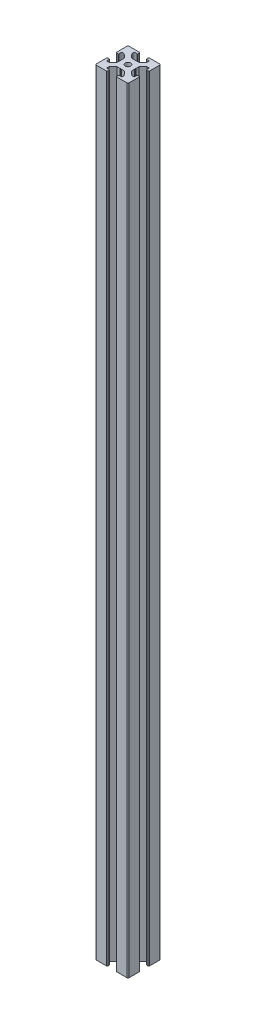
SolidWorks part; units mm, degrees
ref_plane "Front Plane" through (0, 0, 0) normal (0, 0, 1) x (1, 0, 0)
ref_plane "Top Plane" through (0, 0, 0) normal (0, 1, 0) x (1, 0, 0)
ref_plane "Right Plane" through (0, 0, 0) normal (1, 0, 0) x (0, 0, -1)
sketch "Sketch3" plane through (0, 0, 0) normal (0, 1, 0) x (1, 0, 0)
  line L0 (11, 30) -> (11, 27.75)
  line L1 (0, 0) -> (30, 0)
  line L2 (0, 0) -> (0, 30)
  line L3 (0, 30) -> (30, 30)
  line L4 (30, 0) -> (30, 30)
  line L5 (11, 27.75) -> (8, 27.75)
  line L6 (8, 27.75) -> (8, 25.5)
  line L7 (8, 25.5) -> (11.5, 21.75)
  line L8 (11.5, 21.75) -> (18.5, 21.75)
  line L9 (18.5, 21.75) -> (22, 25.5)
  line L10 (22, 25.5) -> (22, 27.75)
  line L11 (22, 27.75) -> (19, 27.75)
  line L12 (19, 27.75) -> (19, 30)
  line L13 (19, 30) -> (11, 30)
  line L14 (14.5, 21.75) -> (15, 21.25)
  line L15 (15, 21.25) -> (15.5, 21.75)
  line L16 (15.5, 21.75) -> (14.5, 21.75)
  line L17 (19, 29.5) -> (19, 30)
  line L18 (19.5, 30) -> (19, 30)
  line L19 (11, 29.5) -> (11, 30)
  line L20 (10.5, 30) -> (11, 30)
  line L21 (0, 19) -> (2.25, 19)
  line L22 (2.25, 19) -> (2.25, 22)
  line L23 (2.25, 22) -> (4.5, 22)
  line L24 (4.5, 22) -> (8.25, 18.5)
  line L25 (8.25, 18.5) -> (8.25, 11.5)
  line L26 (8.25, 11.5) -> (4.5, 8)
  line L27 (4.5, 8) -> (2.25, 8)
  line L28 (2.25, 8) -> (2.25, 11)
  line L29 (2.25, 11) -> (0, 11)
  line L30 (0, 11) -> (0, 19)
  line L31 (8.25, 15.5) -> (8.25, 14.5)
  line L32 (8.25, 14.5) -> (8.75, 15)
  line L33 (8.75, 15) -> (8.25, 15.5)
  line L34 (0.5, 19) -> (0, 19)
  line L35 (0, 19.5) -> (0, 19)
  line L36 (0, 10.5) -> (0, 11)
  line L37 (0.5, 11) -> (0, 11)
  line L38 (15, 30) -> (15, 0) construction
  line L39 (30, 15) -> (0, 15) construction
  line L40 (15, 8.75) -> (15.5, 8.25)
  line L41 (14.5, 8.25) -> (15, 8.75)
  line L42 (15.5, 8.25) -> (14.5, 8.25)
  line L43 (19.5, 0) -> (19, 0)
  line L44 (19, 0.5) -> (19, 0)
  line L45 (10.5, 0) -> (11, 0)
  line L46 (11, 0.5) -> (11, 0)
  line L47 (19, 2.25) -> (19, 0)
  line L48 (22, 2.25) -> (19, 2.25)
  line L49 (22, 4.5) -> (22, 2.25)
  line L50 (18.5, 8.25) -> (22, 4.5)
  line L51 (11.5, 8.25) -> (18.5, 8.25)
  line L52 (8, 4.5) -> (11.5, 8.25)
  line L53 (8, 2.25) -> (8, 4.5)
  line L54 (11, 2.25) -> (8, 2.25)
  line L55 (11, 0) -> (11, 2.25)
  line L56 (19, 0) -> (11, 0)
  line L57 (21.75, 14.5) -> (21.25, 15)
  line L58 (21.75, 15.5) -> (21.75, 14.5)
  line L59 (21.25, 15) -> (21.75, 15.5)
  line L60 (29.5, 11) -> (30, 11)
  line L61 (30, 10.5) -> (30, 11)
  line L62 (30, 19.5) -> (30, 19)
  line L63 (29.5, 19) -> (30, 19)
  line L64 (27.75, 11) -> (30, 11)
  line L65 (27.75, 8) -> (27.75, 11)
  line L66 (25.5, 8) -> (27.75, 8)
  line L67 (21.75, 11.5) -> (25.5, 8)
  line L68 (21.75, 18.5) -> (21.75, 11.5)
  line L69 (25.5, 22) -> (21.75, 18.5)
  line L70 (27.75, 22) -> (25.5, 22)
  line L71 (27.75, 19) -> (27.75, 22)
  line L72 (30, 19) -> (27.75, 19)
  line L73 (30, 11) -> (30, 19)
  arc A0 (19.5, 30) -> (19, 29.5) centre (19, 30) cw
  arc A1 (10.5, 30) -> (11, 29.5) centre (11, 30) ccw
  arc A2 (0.5, 19) -> (0, 19.5) centre (0, 19) ccw
  arc A3 (0.5, 11) -> (0, 10.5) centre (0, 11) cw
  arc A4 (19.5, 0) -> (19, 0.5) centre (19, 0) ccw
  arc A5 (10.5, 0) -> (11, 0.5) centre (11, 0) cw
  arc A6 (29.5, 11) -> (30, 10.5) centre (30, 11) ccw
  arc A7 (29.5, 19) -> (30, 19.5) centre (30, 19) cw
  point P7 (15, 21.75)
  point P16 (15, 30)
  point P26 (8.25, 15)
  point P35 (0, 15)
  dimension "D16" = 0.5
  dimension "D17" = 0.5
  dimension "D28" = 0.5
  dimension "D29" = 0.5
  dimension "D1" = 30
  dimension "D2" = 30
  dimension "D3" = 11
  dimension "D4" = 11
  dimension "D5" = 2.25
  dimension "D6" = 2.25
  dimension "D7" = 3
  dimension "D8" = 3
  dimension "D9" = 2.25
  dimension "D10" = 2.25
  dimension "D11" = 7
  dimension "D12" = 8.25
  dimension "D13" = 0.5
  dimension "D14" = 0.5
  dimension "D15" = 0.5
  dimension "D18" = 11
  dimension "D19" = 11
  dimension "D20" = 2.25
  dimension "D21" = 2.25
  dimension "D22" = 3
  dimension "D23" = 7
  dimension "D24" = 8.25
  dimension "D25" = 0.5
  dimension "D26" = 0.5
  dimension "D27" = 0.5
extrude "Boss-Extrude1" add sketch "Sketch3" along normal blind 710 contours L72 A7 L4 L3 A0 L12 L11 L10 L9 L8 L15 L14 L7 L6 L5 L0 A1 L2 A2 L21 L22 L23 L24 L25 L33 L32 L26 L27 L28 L29 A3 L1 A5 L55 L54 L53 L52 L51 L41 L40 L50 L49 L48 L47 A4
fillet "Fillet1" radius 1 4 edges at (0, 355, 0) (30, 355, 0) (30, 355, -30) (0, 355, -30)
sketch "Sketch4" plane through (0, 710, 0) normal (0, 1, 0) x (1, 0, 0)
  line L0 (18.5, 21.75) -> (8.25, 11.5) construction
  line L1 (21.75, 18.5) -> (11.5, 8.25) construction
  line L2 (15.5, 21.75) -> (21.75, 15.5) construction
  line L9 (8.25, 14.5) -> (14.5, 8.25) construction
  line L10 (8.25, 15.5) -> (14.5, 21.75) construction
  line L11 (21.75, 14.5) -> (15.5, 8.25) construction
  line L12 (11.5, 21.75) -> (21.75, 11.5) construction
  line L13 (8.25, 18.5) -> (18.5, 8.25) construction
  line L20 (30, 15) -> (0, 15) construction
  circle A0 centre (15, 15) radius 2.5
  dimension "D1" = 5
extrude "Cut-Extrude1" cut sketch "Sketch4" against normal through all
fillet "Fillet2" radius 0.5 24 edges at (2.25, 355, -22) (2.25, 355, -19) (8.25, 355, -15.5) (8.25, 355, -14.5) (2.25, 355, -11) (2.25, 355, -8) (8, 355, -2.25) (11, 355, -2.25) (14.5, 355, -8.25) (15.5, 355, -8.25) (19, 355, -2.25) (22, 355, -2.25) (27.75, 355, -8) (27.75, 355, -11) (27.75, 355, -19) (27.75, 355, -22) (21.75, 355, -14.5) (21.75, 355, -15.5) (15.5, 355, -21.75) (14.5, 355, -21.75) (22, 355, -27.75) (19, 355, -27.75) (11, 355, -27.75) (8, 355, -27.75)
